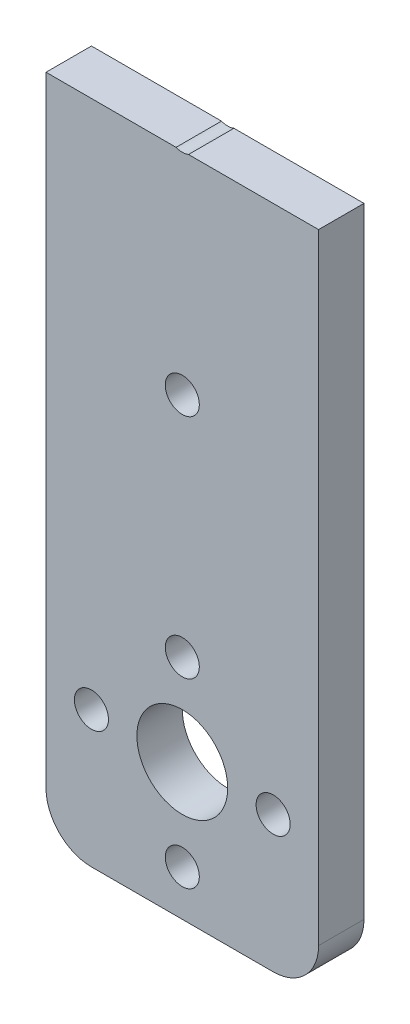
SolidWorks part; units mm, degrees
ref_plane "Front Plane" through (0, 0, 0) normal (0, 0, 1) x (1, 0, 0)
ref_plane "Top Plane" through (0, 0, 0) normal (0, 1, 0) x (1, 0, 0)
ref_plane "Right Plane" through (0, 0, 0) normal (1, 0, 0) x (0, 0, -1)
sketch "Sketch1" plane through (0, 0, 0) normal (0, 0, 1) x (1, 0, 0)
  line L1 (-57.2967, 34.9503) -> (-33.2967, 34.9503)
  line L2 (-57.2967, 34.9503) -> (-57.2967, -45.0497)
  line L3 (-57.2967, -45.0497) -> (-33.2967, -45.0497)
  line L4 (-33.2967, 34.9503) -> (-33.2967, -45.0497)
  dimension "D1" = 80
  dimension "D2" = 24
extrude "Boss-Extrude1" add sketch "Sketch1" along normal blind 4 contours L2 L3 L4 L1
sketch "Sketch2" plane through (0, 0, 4) normal (0, 0, 1) x (1, 0, 0)
  circle A0 centre (-45.2967, -33.0497) radius 4
  circle A1 centre (-37.2967, -33.0497) radius 1.5
  circle A2 centre (-45.2967, -41.0497) radius 1.5
  circle A3 centre (-45.2967, -33.0497) radius 4
  circle A4 centre (-53.2967, -33.0497) radius 1.5
  circle A5 centre (-45.2967, -33.0497) radius 4
  circle A6 centre (-45.2967, -25.0497) radius 1.5
  circle A7 centre (-45.2967, -33.0497) radius 4
  circle A18 centre (-45.2967, 30.9503) radius 1.5
  circle A19 centre (-37.2967, 22.9503) radius 1.5
  circle A20 centre (-45.2967, 14.9503) radius 1.5
  circle A21 centre (-53.2967, 22.9503) radius 1.5
  circle A22 centre (-45.2967, 22.9503) radius 4
  point P21 (-45.2967, -17.0497)
extrude "Cut-Extrude1" cut sketch "Sketch2" against normal blind 4 contours A6 | A0 | A1 | A2 | A4 | A21 | A18 | A22 | A19 | A20
fillet "Fillet1" radius 4 4 edges at (-57.2967, -45.0497, 2) (-33.2967, -45.0497, 2) (-57.2967, 34.9503, 2) (-33.2967, 34.9503, 2)
sketch "Sketch3" plane through (0, 0, 4) normal (0, 0, 1) x (1, 0, 0)
  circle A0 centre (-45.2967, -5.0497) radius 1.5
  circle A1 centre (-45.2967, 22.9503) radius 4 construction
  dimension "D1" = 28
extrude "Cut-Extrude2" cut sketch "Sketch3" against normal blind 4 contours A0
sketch "Sketch4" plane through (0, 0, 4) normal (0, 0, 1) x (1, 0, 0)
  line L0 (-57.2967, 30.9503) -> (-57.2967, -41.0497) construction
  line L1 (-57.2967, 13.5536) -> (-33.2967, 13.5536)
  line L2 (-57.2967, 13.5536) -> (-57.2967, 34.9503)
  line L3 (-57.2967, 34.9503) -> (-33.2967, 34.9503)
  line L4 (-33.2967, 13.5536) -> (-33.2967, 34.9503)
  line L5 (-33.2967, 30.9503) -> (-33.2967, -41.0497) construction
extrude "Cut-Extrude3" cut sketch "Sketch4" against normal blind 4
